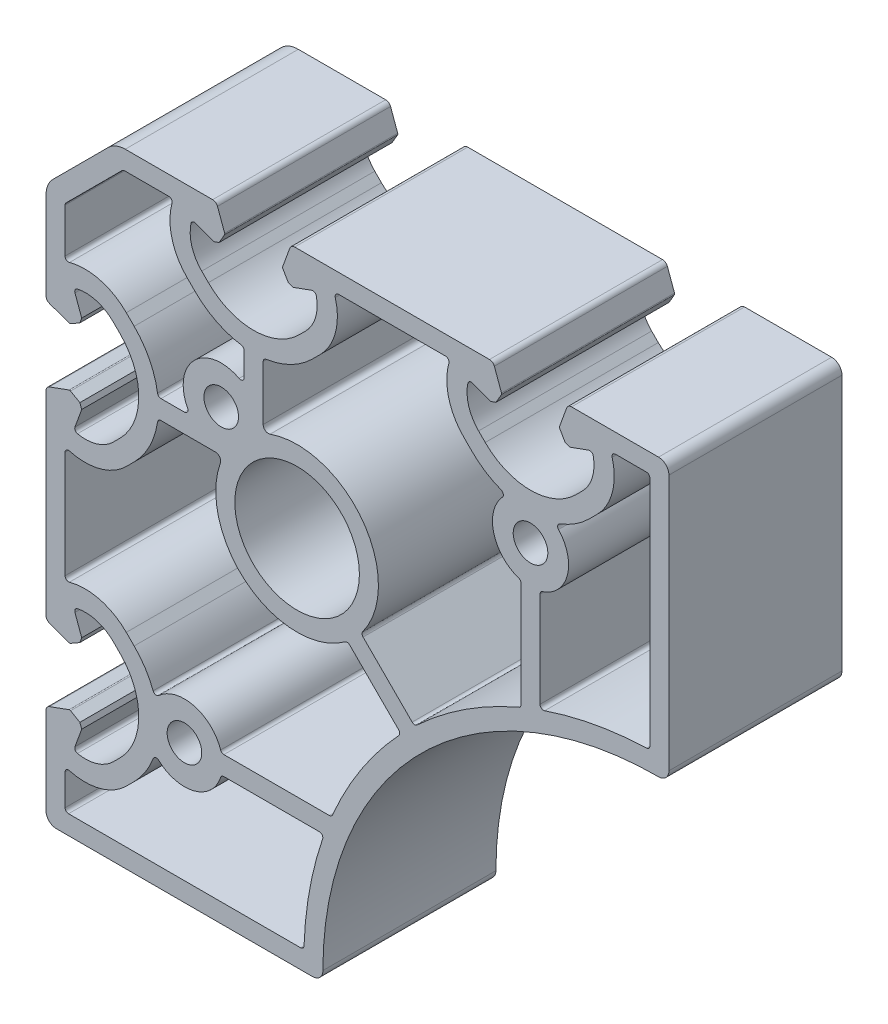
SolidWorks part; units mm, degrees
material "6005-T5"
ref_plane "Front" through (0, 0, 0) normal (0, 0, 1) x (1, 0, 0)
ref_plane "Top" through (0, 0, 0) normal (0, 1, 0) x (1, 0, 0)
ref_plane "Right" through (0, 0, 0) normal (1, 0, 0) x (0, 0, -1)
sketch "Sk Main Extrusion" plane through (0, 0, 0) normal (0, 0, 1) x (1, 0, 0)
  line L86 (43.3447, 24.6769) -> (42.2089, 23.5411)
  line L87 (35.0986, 10.5769) -> (35.0986, -3.2167)
  line L88 (50.9736, -0.5032) -> (50.9736, 33.0264)
  line L89 (50.4736, 33.5264) -> (45.9989, 33.5264)
  line L90 (21.4483, 33.5264) -> (5.9989, 33.5264)
  line L91 (3.3447, 24.6769) -> (2.2089, 23.5411)
  line L92 (-4.9014, 19.6678) -> (-4.9014, 11.7905)
  line L93 (9.5323, -7.5877) -> (16.6271, -14.6826)
  line L94 (32.3486, -4.6534) -> (32.3486, 10.5769)
  line L95 (25.2383, 23.5411) -> (24.1025, 24.6769)
  line L96 (-14.7617, 23.5411) -> (-15.8975, 24.6769)
  line L97 (-18.5517, 33.5264) -> (-24.9302, 33.5264)
  line L98 (-25.2838, 33.38) -> (-33.38, 25.2838)
  line L99 (-33.5264, 24.9302) -> (-33.5264, 18.5517)
  line L100 (-24.6769, 15.8975) -> (-23.5411, 14.7617)
  line L101 (-19.6678, 7.6514) -> (-16.2621, 7.6514)
  line L102 (-7.6514, 16.2621) -> (-7.6514, 19.6678)
  line L103 (-23.5411, -2.2089) -> (-24.6769, -3.3447)
  line L104 (-33.5264, -5.9989) -> (-33.5264, -21.4483)
  line L105 (-24.6769, -24.1025) -> (-23.5411, -25.2383)
  line L106 (-10.5769, -32.3486) -> (4.6534, -32.3486)
  line L107 (14.6826, -16.6271) -> (7.5877, -9.5323)
  line L108 (-11.7905, 4.9014) -> (-19.6678, 4.9014)
  line L109 (-12.2032, 36.2764) -> (-24.8267, 36.2764)
  line L110 (-27.3015, 35.2513) -> (-35.2513, 27.3015)
  line L111 (-36.2764, 24.8267) -> (-36.2764, 12.2032)
  line L112 (-35.7829, 11.4985) -> (-32.9476, 10.4665)
  line L113 (-32.7371, 10.4849) -> (-31.3877, 11.264)
  line L114 (-31.3877, 11.264) -> (-31.1217, 11.9949)
  line L115 (-31.1217, 11.9949) -> (-32.0962, 14.6726)
  line L116 (-26.5491, 13.7806) -> (-25.5857, 12.8171)
  line L117 (-25.5857, -0.2643) -> (-26.5491, -1.2278)
  line L118 (-32.0962, -2.1198) -> (-31.1217, 0.5579)
  line L119 (-31.1217, 0.5579) -> (-31.3877, 1.2888)
  line L120 (-31.3877, 1.2888) -> (-32.7371, 2.0679)
  line L121 (-32.9476, 2.0863) -> (-35.7829, 1.0543)
  line L122 (-36.2764, 0.3496) -> (-36.2764, -27.7968)
  line L123 (-35.7829, -28.5015) -> (-32.9476, -29.5335)
  line L124 (-32.7371, -29.5151) -> (-31.3877, -28.736)
  line L125 (-31.3877, -28.736) -> (-31.1217, -28.0051)
  line L126 (-31.1217, -28.0051) -> (-32.0962, -25.3274)
  line L127 (-26.5491, -26.2194) -> (-25.5857, -27.1829)
  line L128 (-25.5857, -40.2643) -> (-26.5491, -41.2278)
  line L129 (-32.0962, -42.1198) -> (-31.1217, -39.4421)
  line L130 (-31.1217, -39.4421) -> (-31.3877, -38.7112)
  line L131 (-31.3877, -38.7112) -> (-32.7371, -37.9321)
  line L132 (-32.9476, -37.9137) -> (-35.7829, -38.9457)
  line L133 (-36.2764, -39.6504) -> (-36.2764, -52.2236)
  line L134 (-34.7764, -53.7236) -> (2.2236, -53.7236)
  line L135 (53.7236, -2.2236) -> (53.7236, 34.7764)
  line L136 (52.2236, 36.2764) -> (39.6504, 36.2764)
  line L137 (38.9457, 35.7829) -> (37.9137, 32.9476)
  line L138 (37.9321, 32.7371) -> (38.7112, 31.3877)
  line L139 (38.7112, 31.3877) -> (39.4421, 31.1217)
  line L140 (39.4421, 31.1217) -> (42.1198, 32.0962)
  line L141 (41.2278, 26.5491) -> (40.2643, 25.5857)
  line L142 (27.1829, 25.5857) -> (26.2194, 26.5491)
  line L143 (25.3274, 32.0962) -> (28.0051, 31.1217)
  line L144 (28.0051, 31.1217) -> (28.736, 31.3877)
  line L145 (28.736, 31.3877) -> (29.5151, 32.7371)
  line L146 (29.5335, 32.9476) -> (28.5015, 35.7829)
  line L147 (27.7968, 36.2764) -> (-0.3496, 36.2764)
  line L148 (-1.0543, 35.7829) -> (-2.0863, 32.9476)
  line L149 (-2.0679, 32.7371) -> (-1.2888, 31.3877)
  line L150 (-1.2888, 31.3877) -> (-0.5579, 31.1217)
  line L151 (-0.5579, 31.1217) -> (2.1198, 32.0962)
  line L152 (1.2278, 26.5491) -> (0.2643, 25.5857)
  line L153 (-12.8171, 25.5857) -> (-13.7806, 26.5491)
  line L154 (-14.6726, 32.0962) -> (-11.9949, 31.1217)
  line L155 (-11.9949, 31.1217) -> (-11.264, 31.3877)
  line L156 (-11.264, 31.3877) -> (-10.4849, 32.7371)
  line L157 (-10.4665, 32.9476) -> (-11.4985, 35.7829)
  line L158 (-23.5411, -42.2089) -> (-24.6769, -43.3447)
  line L159 (-33.5264, -45.9989) -> (-33.5264, -50.4736)
  line L160 (-33.0264, -50.9736) -> (0.5032, -50.9736)
  line L161 (3.2167, -35.0986) -> (-10.5769, -35.0986)
  arc A112 (37.9668, 20.8016) -> (42.2089, 23.5411) centre (33.7236, 32.0264) ccw
  arc A113 (37.9668, 20.8016) -> (37.7753, 19.9958) centre (38.1436, 20.3339) ccw
  arc A114 (35.4423, 11.0519) -> (37.7753, 19.9958) centre (33.7236, 16.2764) ccw
  arc A115 (35.4423, 11.0519) -> (35.0986, 10.5769) centre (35.5986, 10.5769) ccw
  arc A116 (35.0986, -3.2167) -> (35.7592, -3.6902) centre (35.5986, -3.2167) ccw
  arc A117 (50.4905, -1.0029) -> (35.7592, -3.6902) centre (52.2236, -52.2236) ccw
  arc A118 (50.4905, -1.0029) -> (50.9736, -0.5032) centre (50.4736, -0.5032) ccw
  arc A119 (50.9736, 33.0264) -> (50.4736, 33.5264) centre (50.4736, 33.0264) ccw
  arc A120 (45.9989, 33.5264) -> (45.5168, 32.8937) centre (45.9989, 33.0264) ccw
  arc A121 (43.3447, 24.6769) -> (45.5168, 32.8937) centre (37.3696, 30.6519) ccw
  arc A122 (21.9304, 32.8937) -> (24.1025, 24.6769) centre (30.0776, 30.6519) ccw
  arc A123 (21.9304, 32.8937) -> (21.4483, 33.5264) centre (21.4483, 33.0264) ccw
  arc A124 (5.9989, 33.5264) -> (5.5168, 32.8937) centre (5.9989, 33.0264) ccw
  arc A125 (3.3447, 24.6769) -> (5.5168, 32.8937) centre (-2.6304, 30.6519) ccw
  arc A126 (-4.4764, 20.1622) -> (2.2089, 23.5411) centre (-6.2764, 32.0264) ccw
  arc A127 (-4.4764, 20.1622) -> (-4.9014, 19.6678) centre (-4.4014, 19.6678) ccw
  arc A128 (-4.9014, 11.7905) -> (-3.9023, 11.0831) centre (-4.1514, 11.7905) ccw
  arc A129 (-11.4985, 35.7829) -> (-12.2032, 36.2764) centre (-12.2032, 35.5264) ccw
  arc A130 (-24.8267, 36.2764) -> (-27.3015, 35.2513) centre (-24.8267, 32.7764) ccw
  arc A131 (-35.2513, 27.3015) -> (-36.2764, 24.8267) centre (-32.7764, 24.8267) ccw
  arc A132 (-36.2764, 12.2032) -> (-35.7829, 11.4985) centre (-35.5264, 12.2032) ccw
  arc A133 (-32.9476, 10.4665) -> (-32.7371, 10.4849) centre (-32.8621, 10.7014) ccw
  arc A134 (-31.7271, 15.3334) -> (-32.0962, 14.6726) centre (-31.6264, 14.8436) ccw
  arc A135 (-26.5491, 13.7806) -> (-31.7271, 15.3334) centre (-30.5796, 9.7501) ccw
  arc A136 (-25.5857, -0.2643) -> (-25.5857, 12.8171) centre (-32.1264, 6.2764) ccw
  arc A137 (-31.7271, -2.7806) -> (-26.5491, -1.2278) centre (-30.5796, 2.8027) ccw
  arc A138 (-32.0962, -2.1198) -> (-31.7271, -2.7806) centre (-31.6264, -2.2908) ccw
  arc A139 (-32.7371, 2.0679) -> (-32.9476, 2.0863) centre (-32.8621, 1.8514) ccw
  arc A140 (-35.7829, 1.0543) -> (-36.2764, 0.3496) centre (-35.5264, 0.3496) ccw
  arc A141 (-36.2764, -27.7968) -> (-35.7829, -28.5015) centre (-35.5264, -27.7968) ccw
  arc A142 (-32.9476, -29.5335) -> (-32.7371, -29.5151) centre (-32.8621, -29.2986) ccw
  arc A143 (-31.7271, -24.6666) -> (-32.0962, -25.3274) centre (-31.6264, -25.1564) ccw
  arc A144 (-26.5491, -26.2194) -> (-31.7271, -24.6666) centre (-30.5796, -30.2499) ccw
  arc A145 (-25.5857, -40.2643) -> (-25.5857, -27.1829) centre (-32.1264, -33.7236) ccw
  arc A146 (-31.7271, -42.7806) -> (-26.5491, -41.2278) centre (-30.5796, -37.1973) ccw
  arc A147 (-32.0962, -42.1198) -> (-31.7271, -42.7806) centre (-31.6264, -42.2908) ccw
  arc A148 (-32.7371, -37.9321) -> (-32.9476, -37.9137) centre (-32.8621, -38.1486) ccw
  arc A149 (-35.7829, -38.9457) -> (-36.2764, -39.6504) centre (-35.5264, -39.6504) ccw
  arc A150 (-36.2764, -52.2236) -> (-34.7764, -53.7236) centre (-34.7764, -52.2236) ccw
  arc A151 (2.2236, -53.7236) -> (3.7236, -52.2236) centre (2.2236, -52.2236) ccw
  arc A152 (52.2236, -3.7236) -> (3.7236, -52.2236) centre (52.2236, -52.2236) ccw
  arc A153 (52.2236, -3.7236) -> (53.7236, -2.2236) centre (52.2236, -2.2236) ccw
  arc A154 (53.7236, 34.7764) -> (52.2236, 36.2764) centre (52.2236, 34.7764) ccw
  arc A155 (39.6504, 36.2764) -> (38.9457, 35.7829) centre (39.6504, 35.5264) ccw
  arc A156 (37.9137, 32.9476) -> (37.9321, 32.7371) centre (38.1486, 32.8621) ccw
  arc A157 (42.7806, 31.7271) -> (42.1198, 32.0962) centre (42.2908, 31.6264) ccw
  arc A158 (41.2278, 26.5491) -> (42.7806, 31.7271) centre (37.1973, 30.5796) ccw
  arc A159 (27.1829, 25.5857) -> (40.2643, 25.5857) centre (33.7236, 32.1264) ccw
  arc A160 (24.6666, 31.7271) -> (26.2194, 26.5491) centre (30.2499, 30.5796) ccw
  arc A161 (25.3274, 32.0962) -> (24.6666, 31.7271) centre (25.1564, 31.6264) ccw
  arc A162 (29.5151, 32.7371) -> (29.5335, 32.9476) centre (29.2986, 32.8621) ccw
  arc A163 (28.5015, 35.7829) -> (27.7968, 36.2764) centre (27.7968, 35.5264) ccw
  arc A164 (-0.3496, 36.2764) -> (-1.0543, 35.7829) centre (-0.3496, 35.5264) ccw
  arc A165 (-2.0863, 32.9476) -> (-2.0679, 32.7371) centre (-1.8514, 32.8621) ccw
  arc A166 (2.7806, 31.7271) -> (2.1198, 32.0962) centre (2.2908, 31.6264) ccw
  arc A167 (1.2278, 26.5491) -> (2.7806, 31.7271) centre (-2.8027, 30.5796) ccw
  arc A168 (-12.8171, 25.5857) -> (0.2643, 25.5857) centre (-6.2764, 32.1264) ccw
  arc A169 (-15.3334, 31.7271) -> (-13.7806, 26.5491) centre (-9.7501, 30.5796) ccw
  arc A170 (-14.6726, 32.0962) -> (-15.3334, 31.7271) centre (-14.8436, 31.6264) ccw
  arc A171 (-10.4849, 32.7371) -> (-10.4665, 32.9476) centre (-10.7014, 32.8621) ccw
  arc A172 (9.4823, -6.9389) -> (-3.9023, 11.0831) centre (0, 0) ccw
  arc A173 (9.4823, -6.9389) -> (9.5323, -7.5877) centre (9.8858, -7.2342) ccw
  arc A174 (16.6271, -14.6826) -> (17.3212, -14.6952) centre (16.9807, -14.329) ccw
  arc A175 (32.0455, -5.113) -> (17.3212, -14.6952) centre (52.2236, -52.2236) ccw
  arc A176 (32.0455, -5.113) -> (32.3486, -4.6534) centre (31.8486, -4.6534) ccw
  arc A177 (32.3486, 10.5769) -> (32.0048, 11.0519) centre (31.8486, 10.5769) ccw
  arc A178 (29.6719, 19.9958) -> (32.0048, 11.0519) centre (33.7236, 16.2764) ccw
  arc A179 (29.6719, 19.9958) -> (29.4804, 20.8016) centre (29.3036, 20.3339) ccw
  arc A180 (25.2383, 23.5411) -> (29.4804, 20.8016) centre (33.7236, 32.0264) ccw
  arc A181 (-18.0696, 32.8937) -> (-15.8975, 24.6769) centre (-9.9224, 30.6519) ccw
  arc A182 (-18.0696, 32.8937) -> (-18.5517, 33.5264) centre (-18.5517, 33.0264) ccw
  arc A183 (-24.9302, 33.5264) -> (-25.2838, 33.38) centre (-24.9302, 33.0264) ccw
  arc A184 (-33.38, 25.2838) -> (-33.5264, 24.9302) centre (-33.0264, 24.9302) ccw
  arc A185 (-33.5264, 18.5517) -> (-32.8937, 18.0696) centre (-33.0264, 18.5517) ccw
  arc A186 (-24.6769, 15.8975) -> (-32.8937, 18.0696) centre (-30.6519, 9.9224) ccw
  arc A187 (-20.1622, 8.0764) -> (-23.5411, 14.7617) centre (-32.0264, 6.2764) ccw
  arc A188 (-20.1622, 8.0764) -> (-19.6678, 7.6514) centre (-19.6678, 8.1514) ccw
  arc A189 (-16.2621, 7.6514) -> (-15.8203, 8.3855) centre (-16.2621, 8.1514) ccw
  arc A190 (-8.3855, 15.8203) -> (-15.8203, 8.3855) centre (-10.9602, 10.9602) ccw
  arc A191 (-8.3855, 15.8203) -> (-7.6514, 16.2621) centre (-8.1514, 16.2621) ccw
  arc A192 (-7.6514, 19.6678) -> (-8.0764, 20.1622) centre (-8.1514, 19.6678) ccw
  arc A193 (-14.7617, 23.5411) -> (-8.0764, 20.1622) centre (-6.2764, 32.0264) ccw
  arc A194 (-19.6678, 4.9014) -> (-20.1622, 4.4764) centre (-19.6678, 4.4014) ccw
  arc A195 (-23.5411, -2.2089) -> (-20.1622, 4.4764) centre (-32.0264, 6.2764) ccw
  arc A196 (-32.8937, -5.5168) -> (-24.6769, -3.3447) centre (-30.6519, 2.6304) ccw
  arc A197 (-32.8937, -5.5168) -> (-33.5264, -5.9989) centre (-33.0264, -5.9989) ccw
  arc A198 (-33.5264, -21.4483) -> (-32.8937, -21.9304) centre (-33.0264, -21.4483) ccw
  arc A199 (-24.6769, -24.1025) -> (-32.8937, -21.9304) centre (-30.6519, -30.0776) ccw
  arc A200 (-20.8016, -29.4804) -> (-23.5411, -25.2383) centre (-32.0264, -33.7236) ccw
  arc A201 (-20.8016, -29.4804) -> (-19.9958, -29.6719) centre (-20.3339, -29.3036) ccw
  arc A202 (-11.0519, -32.0048) -> (-19.9958, -29.6719) centre (-16.2764, -33.7236) ccw
  arc A203 (-11.0519, -32.0048) -> (-10.5769, -32.3486) centre (-10.5769, -31.8486) ccw
  arc A204 (4.6534, -32.3486) -> (5.113, -32.0455) centre (4.6534, -31.8486) ccw
  arc A205 (14.6952, -17.3212) -> (5.113, -32.0455) centre (52.2236, -52.2236) ccw
  arc A206 (14.6952, -17.3212) -> (14.6826, -16.6271) centre (14.329, -16.9807) ccw
  arc A207 (7.5877, -9.5323) -> (6.9389, -9.4823) centre (7.2342, -9.8858) ccw
  arc A208 (-11.0831, 3.9023) -> (6.9389, -9.4823) centre (0, 0) ccw
  arc A209 (-11.0831, 3.9023) -> (-11.7905, 4.9014) centre (-11.7905, 4.1514) ccw
  arc A210 (-10.5769, -35.0986) -> (-11.0519, -35.4424) centre (-10.5769, -35.5986) ccw
  arc A211 (-19.9958, -37.7753) -> (-11.0519, -35.4424) centre (-16.2764, -33.7236) ccw
  arc A212 (-19.9958, -37.7753) -> (-20.8016, -37.9668) centre (-20.3339, -38.1436) ccw
  arc A213 (-23.5411, -42.2089) -> (-20.8016, -37.9668) centre (-32.0264, -33.7236) ccw
  arc A214 (-32.8937, -45.5168) -> (-24.6769, -43.3447) centre (-30.6519, -37.3696) ccw
  arc A215 (-32.8937, -45.5168) -> (-33.5264, -45.9989) centre (-33.0264, -45.9989) ccw
  arc A216 (-33.5264, -50.4736) -> (-33.0264, -50.9736) centre (-33.0264, -50.4736) ccw
  arc A217 (0.5032, -50.9736) -> (1.0029, -50.4905) centre (0.5032, -50.4736) ccw
  arc A218 (3.6902, -35.7592) -> (1.0029, -50.4905) centre (52.2236, -52.2236) ccw
  arc A219 (3.6902, -35.7592) -> (3.2167, -35.0986) centre (3.2167, -35.5986) ccw
  circle A220 centre (-16.2764, -33.7236) radius 2.5
  circle A221 centre (33.7236, 16.2764) radius 2.5
  circle A222 centre (0, 0) radius 9
  circle A223 centre (-10.9602, 10.9602) radius 2.5
  point P300 (8.7236, -8.7236)
extrude "Main Extrusion" add sketch "Sk Main Extrusion" against normal blind 25
sketch "Threaded Insert Mate Sketch" plane through (0, 0, 0) normal (0, 0, 1) x (1, 0, 0)
  line L0 (-12.2032, 36.2764) -> (-0.3496, 36.2764) construction
  line L1 (13.7236, 36.2764) -> (13.7236, -11.7791) construction
  line L3 (-31.2764, 31.2764) -> (0, 0) construction
  line L6 (27.7968, 36.2764) -> (-0.3496, 36.2764) construction
  line L7 (9.5323, -7.5877) -> (16.6271, -14.6826) construction
  line L8 (-27.3015, 35.2513) -> (-35.2513, 27.3015) construction
  circle A0 centre (-6.2764, 28.9764) radius 5.6515
  circle A1 centre (33.7236, 28.9764) radius 5.6515
  circle A2 centre (-28.9764, -33.7236) radius 5.6515
  circle A3 centre (-28.9764, 6.2764) radius 5.6515
  point P3 (-6.2764, 36.2764)
  point P12 (13.7236, 36.2764)
  point P15 (0, 0)
  point P18 (0, 0)
  point P19 (0, 0)
  point P26 (0, 0)
  point P27 (0, 0)
  point P29 (0, 0)
  point P31 (0, 0)
  point P33 (0, 0)
  point P34 (0, 0)
  point P35 (-12.2032, 36.2764)
  point P37 (-0.3496, 36.2764)
  dimension "D2" = 11.303
  dimension "D1" = 7.3
equation "\"Weight kg\"= round ( \"SW-Mass\" , 2 )"
equation "\"Weight lbs\"= round ( \"SW-Mass\" * 2.2046 , 2 )"
equation "\"Length mm\"= round ( \"Length@Main Extrusion\" , 2 )"
equation "\"Length in\"= round ( \"Length@Main Extrusion\" / 25.4 , 3 )"
